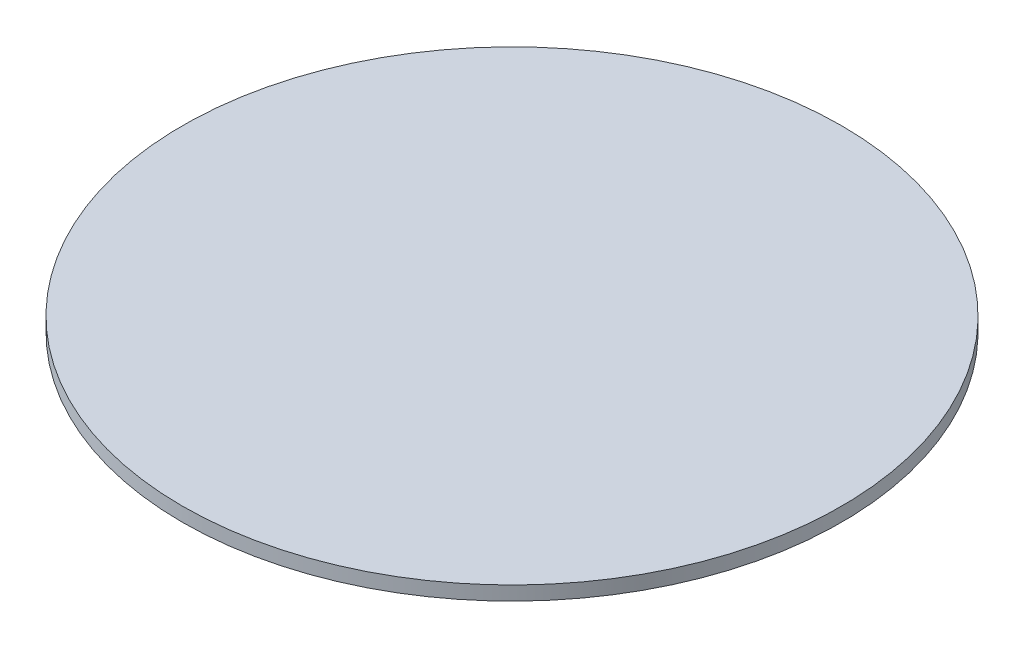
SolidWorks part; units mm, degrees
ref_plane "Front Plane" through (0, 0, 0) normal (0, 0, 1) x (1, 0, 0)
ref_plane "Top Plane" through (0, 0, 0) normal (0, 1, 0) x (1, 0, 0)
ref_plane "Right Plane" through (0, 0, 0) normal (1, 0, 0) x (0, 0, -1)
sketch "Sketch1" plane through (0, 0, 0) normal (0, 1, 0) x (1, 0, 0)
  circle A0 centre (0, 0) radius 40
extrude "Boss-Extrude1" add sketch "Sketch1" along normal blind 1.7
scale "Scale1" scale about centroid uniform scaling yes scale factor 0.75
